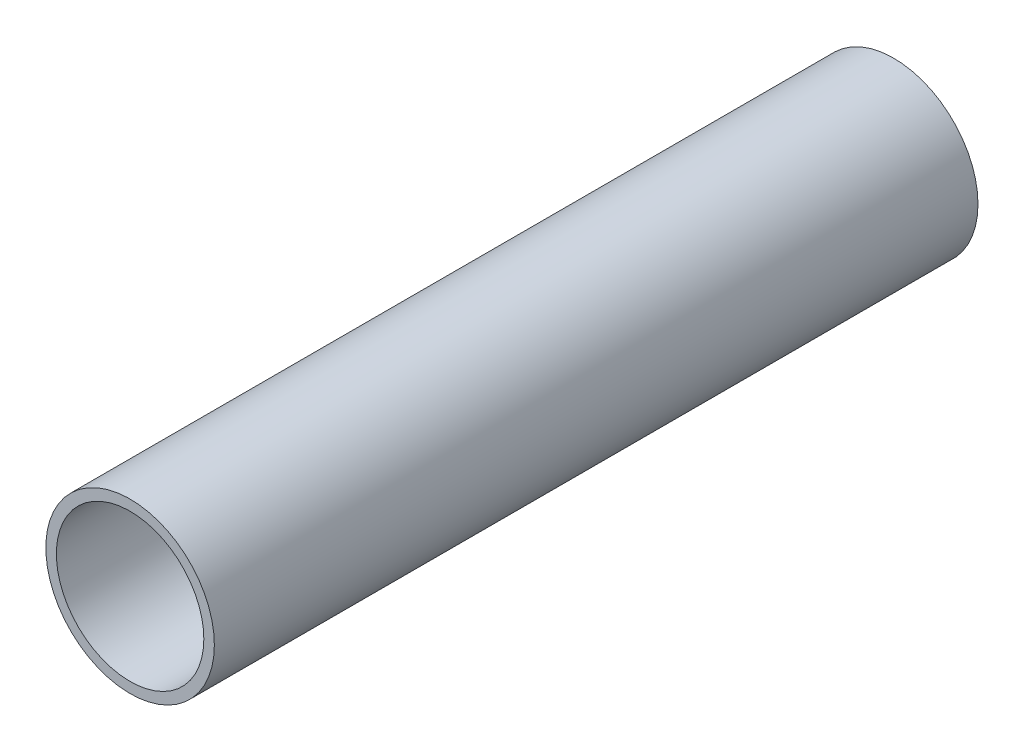
SolidWorks part; units mm, degrees
ref_plane "Front Plane" through (0, 0, 0) normal (0, 0, 1) x (1, 0, 0)
ref_plane "Top Plane" through (0, 0, 0) normal (0, 1, 0) x (1, 0, 0)
ref_plane "Right Plane" through (0, 0, 0) normal (1, 0, 0) x (0, 0, -1)
sketch "Sketch1" plane through (0, 0, 0) normal (0, 0, 1) x (1, 0, 0)
  circle A0 centre (0, 0) radius 14
  circle A1 centre (0, 0) radius 16
  dimension "D1" = 28
  dimension "D2" = 32
extrude "Boss-Extrude1" add sketch "Sketch1" along normal blind 145
